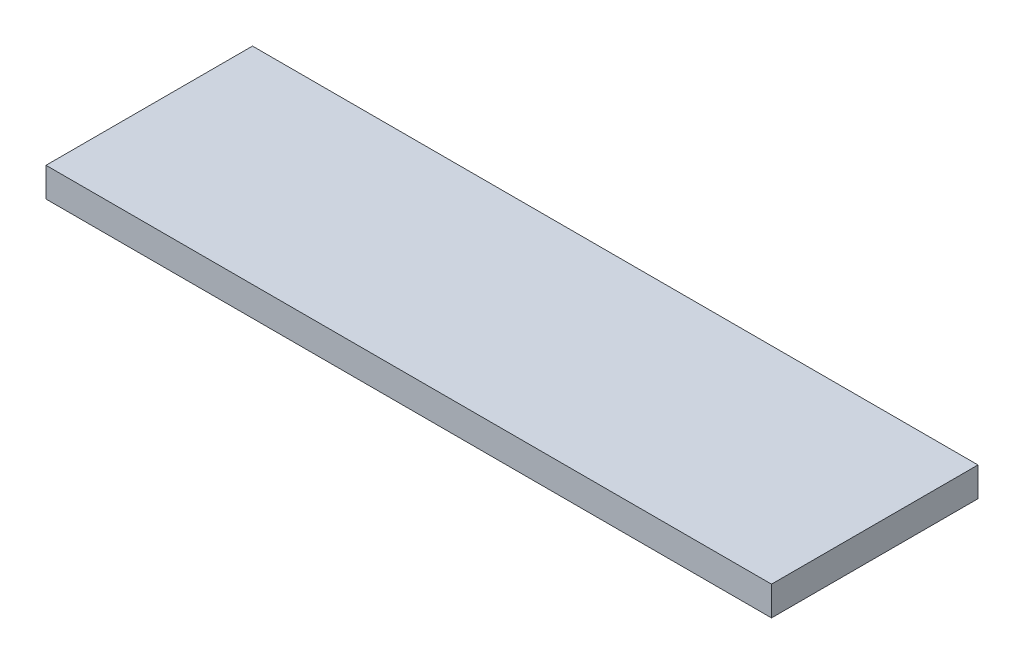
SolidWorks part; units mm, degrees
material "ABS PC"
ref_plane "Plan de face" through (0, 0, 0) normal (0, 0, 1) x (1, 0, 0)
ref_plane "Plan de dessus" through (0, 0, 0) normal (0, 1, 0) x (1, 0, 0)
ref_plane "Plan de droite" through (0, 0, 0) normal (1, 0, 0) x (0, 0, -1)
sketch "Esquisse1" plane through (0, 0, 0) normal (0, 1, 0) x (1, 0, 0)
  line L1 (-39.2021, 23.831) -> (22.7586, 23.831)
  line L2 (-39.2021, 23.831) -> (-39.2021, 6.1961)
  line L3 (-39.2021, 6.1961) -> (22.7586, 6.1961)
  line L4 (22.7586, 23.831) -> (22.7586, 6.1961)
extrude "Boss.-Extru.1" add sketch "Esquisse1" along normal blind 2.5
